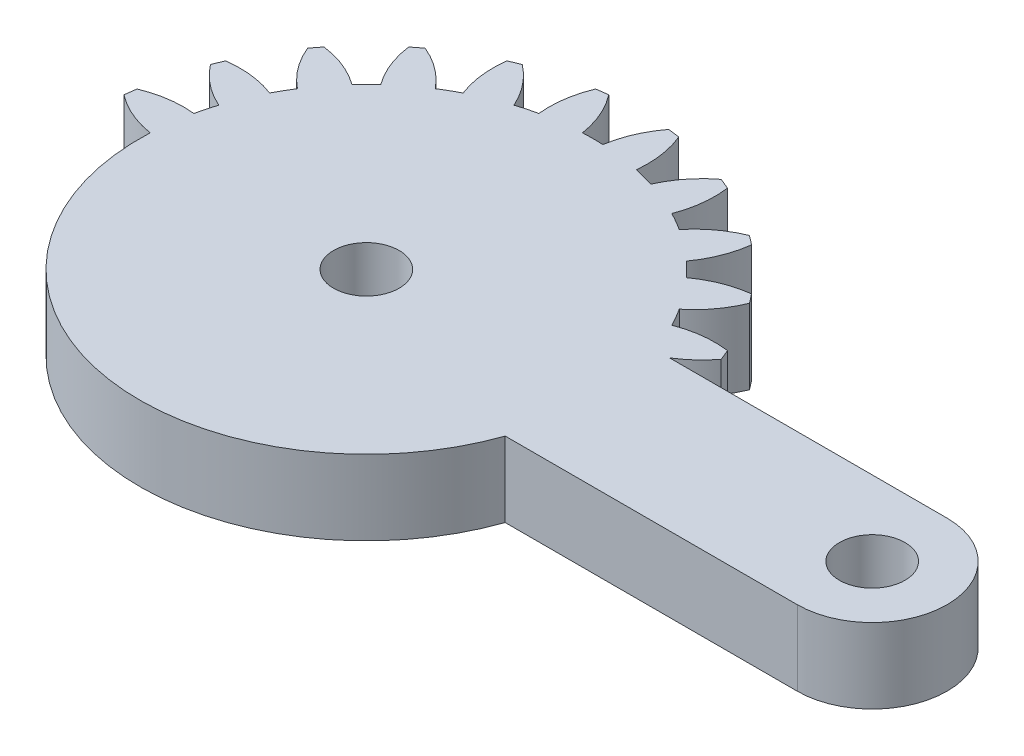
SolidWorks part; units mm, degrees
ref_plane "Front Plane" through (0, 0, 0) normal (0, 0, 1) x (1, 0, 0)
ref_plane "Top Plane" through (0, 0, 0) normal (0, 1, 0) x (1, 0, 0)
ref_plane "Right Plane" through (0, 0, 0) normal (1, 0, 0) x (0, 0, -1)
sketch "Sketch1" plane through (0, 0, 0) normal (0, 1, 0) x (1, 0, 0)
  line L0 (16.8937, 4) -> (2.0816, 4)
  line L1 (2.0816, -4) -> (16.8937, -4)
  line L2 (-10.1063, 0) -> (47.0285, 0) construction
  arc A0 (2.0816, 4) -> (3.5217, 5.3071) centre (-0.7683, 8.5867) ccw
  arc A1 (3.5217, 5.3071) -> (3.2829, 5.8838) centre (-10.1063, 0) ccw
  arc A2 (3.2829, 5.8838) -> (0.6271, 5.5703) centre (2.5684, 0.5313) ccw
  arc A3 (0.6271, 5.5703) -> (0.0844, 6.5103) centre (-10.1063, 0) ccw
  arc A4 (0.0844, 6.5103) -> (1.6838, 8.6535) centre (-3.3089, 10.711) ccw
  arc A5 (1.6838, 8.6535) -> (1.3038, 9.1487) centre (-10.1063, 0) ccw
  arc A6 (1.3038, 9.1487) -> (-1.1803, 8.1585) centre (1.999, 3.7936) ccw
  arc A7 (-1.1803, 8.1585) -> (-1.9479, 8.926) centre (-10.1063, 0) ccw
  arc A8 (-1.9479, 8.926) -> (-0.9576, 11.4102) centre (-6.3127, 12.1053) ccw
  arc A9 (-0.9576, 11.4102) -> (-1.4528, 11.7901) centre (-10.1063, 0) ccw
  arc A10 (-1.4528, 11.7901) -> (-3.596, 10.1907) centre (0.6046, 6.7975) ccw
  arc A11 (-3.596, 10.1907) -> (-4.5361, 10.7334) centre (-10.1063, 0) ccw
  arc A12 (-4.5361, 10.7334) -> (-4.2225, 13.3892) centre (-9.5751, 12.6747) ccw
  arc A13 (-4.2225, 13.3892) -> (-4.7992, 13.6281) centre (-10.1063, 0) ccw
  arc A14 (-4.7992, 13.6281) -> (-6.4554, 11.5285) centre (-1.5196, 9.3381) ccw
  arc A15 (-6.4554, 11.5285) -> (-7.5039, 11.8094) centre (-10.1063, 0) ccw
  arc A16 (-7.5039, 11.8094) -> (-7.8884, 14.4558) centre (-12.8736, 12.3803) ccw
  arc A17 (-7.8884, 14.4558) -> (-8.5072, 14.5373) centre (-10.1063, 0) ccw
  arc A18 (-8.5072, 14.5373) -> (-9.5636, 12.0806) centre (-4.2291, 11.2423) ccw
  arc A19 (-9.5636, 12.0806) -> (-10.6491, 12.0806) centre (-10.1063, 0) ccw
  arc A20 (-10.6491, 12.0806) -> (-11.7054, 14.5373) centre (-15.9836, 11.2423) ccw
  arc A21 (-11.7054, 14.5373) -> (-12.3243, 14.4558) centre (-10.1063, 0) ccw
  arc A22 (-12.3243, 14.4558) -> (-12.7088, 11.8094) centre (-7.3391, 12.3803) ccw
  arc A23 (-12.7088, 11.8094) -> (-13.7573, 11.5285) centre (-10.1063, 0) ccw
  arc A24 (-13.7573, 11.5285) -> (-15.4135, 13.6281) centre (-18.6931, 9.3381) ccw
  arc A25 (-15.4135, 13.6281) -> (-15.9901, 13.3892) centre (-10.1063, 0) ccw
  arc A26 (-15.9901, 13.3892) -> (-15.6766, 10.7334) centre (-10.6376, 12.6747) ccw
  arc A27 (-15.6766, 10.7334) -> (-16.6166, 10.1907) centre (-10.1063, 0) ccw
  arc A28 (-16.6166, 10.1907) -> (-18.7599, 11.7901) centre (-20.8173, 6.7975) ccw
  arc A29 (-18.7599, 11.7901) -> (-19.255, 11.4102) centre (-10.1063, 0) ccw
  arc A30 (-19.255, 11.4102) -> (-18.2648, 8.926) centre (-13.9, 12.1053) ccw
  arc A31 (-18.2648, 8.926) -> (-19.0324, 8.1585) centre (-10.1063, 0) ccw
  arc A32 (-19.0324, 8.1585) -> (-21.5165, 9.1487) centre (-22.2117, 3.7936) ccw
  arc A33 (-21.5165, 9.1487) -> (-21.8965, 8.6535) centre (-10.1063, 0) ccw
  arc A34 (-21.8965, 8.6535) -> (-20.2971, 6.5103) centre (-16.9038, 10.711) ccw
  arc A35 (-20.2971, 6.5103) -> (-20.8398, 5.5703) centre (-10.1063, 0) ccw
  arc A36 (-20.8398, 5.5703) -> (-23.4956, 5.8838) centre (-22.7811, 0.5313) ccw
  arc A37 (-23.4956, 5.8838) -> (-23.7344, 5.3071) centre (-10.1063, 0) ccw
  arc A38 (-23.7344, 5.3071) -> (-21.6348, 3.6509) centre (-19.4444, 8.5867) ccw
  arc A39 (-21.6348, 3.6509) -> (-21.9157, 2.6025) centre (-10.1063, 0) ccw
  arc A40 (-21.9157, 2.6025) -> (-24.5622, 2.2179) centre (-22.4867, -2.7673) ccw
  arc A41 (-24.5622, 2.2179) -> (-24.6437, 1.5991) centre (-10.1063, 0) ccw
  arc A42 (-24.6437, 1.5991) -> (-22.1869, 0.5427) centre (-21.3486, 5.8773) ccw
  arc A43 (-22.1869, 0.5427) -> (-22.1869, -0.5427) centre (-10.1063, 0) ccw
  arc A44 (-22.1869, -0.5427) -> (-24.6437, -1.5991) centre (-21.3486, -5.8773) ccw
  arc A45 (-24.6437, -1.5991) -> (-24.5622, -2.2179) centre (-10.1063, 0) ccw
  arc A46 (-24.5622, -2.2179) -> (-21.9157, -2.6025) centre (-22.4867, 2.7673) ccw
  arc A47 (-21.9157, -2.6025) -> (-21.6348, -3.6509) centre (-10.1063, 0) ccw
  arc A48 (-21.6348, -3.6509) -> (-23.7344, -5.3071) centre (-19.4444, -8.5867) ccw
  arc A49 (-23.7344, -5.3071) -> (-23.4956, -5.8838) centre (-10.1063, 0) ccw
  arc A50 (-23.4956, -5.8838) -> (-20.8398, -5.5703) centre (-22.7811, -0.5313) ccw
  arc A51 (-20.8398, -5.5703) -> (-20.2971, -6.5103) centre (-10.1063, 0) ccw
  arc A52 (-20.2971, -6.5103) -> (-21.8965, -8.6535) centre (-16.9038, -10.711) ccw
  arc A53 (-21.8965, -8.6535) -> (-21.5165, -9.1487) centre (-10.1063, 0) ccw
  arc A54 (-21.5165, -9.1487) -> (-19.0324, -8.1585) centre (-22.2117, -3.7936) ccw
  arc A55 (-19.0324, -8.1585) -> (-18.2648, -8.926) centre (-10.1063, 0) ccw
  arc A56 (-18.2648, -8.926) -> (-19.255, -11.4102) centre (-13.9, -12.1053) ccw
  arc A57 (-19.255, -11.4102) -> (-18.7599, -11.7901) centre (-10.1063, 0) ccw
  arc A58 (-18.7599, -11.7901) -> (-16.6166, -10.1907) centre (-20.8173, -6.7975) ccw
  arc A59 (-16.6166, -10.1907) -> (-15.6766, -10.7334) centre (-10.1063, 0) ccw
  arc A60 (-15.6766, -10.7334) -> (-15.9901, -13.3892) centre (-10.6376, -12.6747) ccw
  arc A61 (-15.9901, -13.3892) -> (-15.4135, -13.6281) centre (-10.1063, 0) ccw
  arc A62 (-15.4135, -13.6281) -> (-13.7573, -11.5285) centre (-18.6931, -9.3381) ccw
  arc A63 (-13.7573, -11.5285) -> (-12.7088, -11.8094) centre (-10.1063, 0) ccw
  arc A64 (-12.7088, -11.8094) -> (-12.3243, -14.4558) centre (-7.3391, -12.3803) ccw
  arc A65 (-12.3243, -14.4558) -> (-11.7054, -14.5373) centre (-10.1063, 0) ccw
  arc A66 (-11.7054, -14.5373) -> (-10.6491, -12.0806) centre (-15.9836, -11.2423) ccw
  arc A67 (-10.6491, -12.0806) -> (-9.5636, -12.0806) centre (-10.1063, 0) ccw
  arc A68 (-9.5636, -12.0806) -> (-8.5072, -14.5373) centre (-4.2291, -11.2423) ccw
  arc A69 (-8.5072, -14.5373) -> (-7.8884, -14.4558) centre (-10.1063, 0) ccw
  arc A70 (-7.8884, -14.4558) -> (-7.5039, -11.8094) centre (-12.8736, -12.3803) ccw
  arc A71 (-7.5039, -11.8094) -> (-6.4554, -11.5285) centre (-10.1063, 0) ccw
  arc A72 (-6.4554, -11.5285) -> (-4.7992, -13.6281) centre (-1.5196, -9.3381) ccw
  arc A73 (-4.7992, -13.6281) -> (-4.2225, -13.3892) centre (-10.1063, 0) ccw
  arc A74 (-4.2225, -13.3892) -> (-4.5361, -10.7334) centre (-9.5751, -12.6747) ccw
  arc A75 (-4.5361, -10.7334) -> (-3.596, -10.1907) centre (-10.1063, 0) ccw
  arc A76 (-3.596, -10.1907) -> (-1.4528, -11.7901) centre (0.6046, -6.7975) ccw
  arc A77 (-1.4528, -11.7901) -> (-0.9576, -11.4102) centre (-10.1063, 0) ccw
  arc A78 (-0.9576, -11.4102) -> (-1.9479, -8.926) centre (-6.3127, -12.1053) ccw
  arc A79 (-1.9479, -8.926) -> (-1.1803, -8.1585) centre (-10.1063, 0) ccw
  arc A80 (-1.1803, -8.1585) -> (1.3038, -9.1487) centre (1.999, -3.7936) ccw
  arc A81 (1.3038, -9.1487) -> (1.6838, -8.6535) centre (-10.1063, 0) ccw
  arc A82 (1.6838, -8.6535) -> (0.0844, -6.5103) centre (-3.3089, -10.711) ccw
  arc A83 (0.0844, -6.5103) -> (0.6271, -5.5703) centre (-10.1063, 0) ccw
  arc A84 (0.6271, -5.5703) -> (3.2829, -5.8838) centre (2.5684, -0.5313) ccw
  arc A85 (3.2829, -5.8838) -> (3.5217, -5.3071) centre (-10.1063, 0) ccw
  arc A86 (3.5217, -5.3071) -> (2.0816, -4) centre (-0.7683, -8.5867) ccw
  circle A88 centre (-10.1063, 0) radius 1.75
  circle A90 centre (16.8937, 0) radius 1.75
  arc A91 (16.8937, -4) -> (16.8937, 4) centre (16.8937, 0) ccw
  dimension "D1" = 3.5
  dimension "D3" = 3.5
  dimension "D4" = 27
extrude "Boss-Extrude1" add sketch "Sketch1" along normal blind 4
sketch "Sketch2" plane through (0, 4, 0) normal (0, 1, 0) x (1, 0, 0)
  line L0 (2.0816, -4) -> (1.3057, -4)
  line L2 (16.8937, 4) -> (2.0816, 4)
  line L3 (2.0816, -4) -> (16.8937, -4)
  line L4 (16.8937, 4) -> (2.0816, 4)
  line L5 (2.0816, -4) -> (16.8937, -4)
  circle A0 centre (-10.1063, 0) radius 12.0927
  arc A88 (16.8937, -4) -> (16.8937, 4) centre (16.8937, 0) ccw
  arc A89 (2.0816, 4) -> (3.5217, 5.3071) centre (-0.7683, 8.5867) ccw
  arc A90 (3.5217, 5.3071) -> (3.2829, 5.8838) centre (-10.1063, 0) ccw
  arc A91 (3.2829, 5.8838) -> (0.6271, 5.5703) centre (2.5684, 0.5313) ccw
  arc A92 (0.6271, 5.5703) -> (0.0844, 6.5103) centre (-10.1063, 0) ccw
  arc A93 (0.0844, 6.5103) -> (1.6838, 8.6535) centre (-3.3089, 10.711) ccw
  arc A94 (1.6838, 8.6535) -> (1.3038, 9.1487) centre (-10.1063, 0) ccw
  arc A95 (1.3038, 9.1487) -> (-1.1803, 8.1585) centre (1.999, 3.7936) ccw
  arc A96 (-1.1803, 8.1585) -> (-1.9479, 8.926) centre (-10.1063, 0) ccw
  arc A97 (-1.9479, 8.926) -> (-0.9576, 11.4102) centre (-6.3127, 12.1053) ccw
  arc A98 (-0.9576, 11.4102) -> (-1.4528, 11.7901) centre (-10.1063, 0) ccw
  arc A99 (-1.4528, 11.7901) -> (-3.596, 10.1907) centre (0.6046, 6.7975) ccw
  arc A100 (-3.596, 10.1907) -> (-4.5361, 10.7334) centre (-10.1063, 0) ccw
  arc A101 (-4.5361, 10.7334) -> (-4.2225, 13.3892) centre (-9.5751, 12.6747) ccw
  arc A102 (-4.2225, 13.3892) -> (-4.7992, 13.6281) centre (-10.1063, 0) ccw
  arc A103 (-4.7992, 13.6281) -> (-6.4554, 11.5285) centre (-1.5196, 9.3381) ccw
  arc A104 (-6.4554, 11.5285) -> (-7.5039, 11.8094) centre (-10.1063, 0) ccw
  arc A105 (-7.5039, 11.8094) -> (-7.8884, 14.4558) centre (-12.8736, 12.3803) ccw
  arc A106 (-7.8884, 14.4558) -> (-8.5072, 14.5373) centre (-10.1063, 0) ccw
  arc A107 (-8.5072, 14.5373) -> (-9.5636, 12.0806) centre (-4.2291, 11.2423) ccw
  arc A108 (-9.5636, 12.0806) -> (-10.6491, 12.0806) centre (-10.1063, 0) ccw
  arc A109 (-10.6491, 12.0806) -> (-11.7054, 14.5373) centre (-15.9836, 11.2423) ccw
  arc A110 (-11.7054, 14.5373) -> (-12.3243, 14.4558) centre (-10.1063, 0) ccw
  arc A111 (-12.3243, 14.4558) -> (-12.7088, 11.8094) centre (-7.3391, 12.3803) ccw
  arc A112 (-12.7088, 11.8094) -> (-13.7573, 11.5285) centre (-10.1063, 0) ccw
  arc A113 (-13.7573, 11.5285) -> (-15.4135, 13.6281) centre (-18.6931, 9.3381) ccw
  arc A114 (-15.4135, 13.6281) -> (-15.9901, 13.3892) centre (-10.1063, 0) ccw
  arc A115 (-15.9901, 13.3892) -> (-15.6766, 10.7334) centre (-10.6376, 12.6747) ccw
  arc A116 (-15.6766, 10.7334) -> (-16.6166, 10.1907) centre (-10.1063, 0) ccw
  arc A117 (-16.6166, 10.1907) -> (-18.7599, 11.7901) centre (-20.8173, 6.7975) ccw
  arc A118 (-18.7599, 11.7901) -> (-19.255, 11.4102) centre (-10.1063, 0) ccw
  arc A119 (-19.255, 11.4102) -> (-18.2648, 8.926) centre (-13.9, 12.1053) ccw
  arc A120 (-18.2648, 8.926) -> (-19.0324, 8.1585) centre (-10.1063, 0) ccw
  arc A121 (-19.0324, 8.1585) -> (-21.5165, 9.1487) centre (-22.2117, 3.7936) ccw
  arc A122 (-21.5165, 9.1487) -> (-21.8965, 8.6535) centre (-10.1063, 0) ccw
  arc A123 (-21.8965, 8.6535) -> (-20.2971, 6.5103) centre (-16.9038, 10.711) ccw
  arc A124 (-20.2971, 6.5103) -> (-20.8398, 5.5703) centre (-10.1063, 0) ccw
  arc A125 (-20.8398, 5.5703) -> (-23.4956, 5.8838) centre (-22.7811, 0.5313) ccw
  arc A126 (-23.4956, 5.8838) -> (-23.7344, 5.3071) centre (-10.1063, 0) ccw
  arc A127 (-23.7344, 5.3071) -> (-21.6348, 3.6509) centre (-19.4444, 8.5867) ccw
  arc A128 (-21.6348, 3.6509) -> (-21.9157, 2.6025) centre (-10.1063, 0) ccw
  arc A129 (-21.9157, 2.6025) -> (-24.5622, 2.2179) centre (-22.4867, -2.7673) ccw
  arc A130 (-24.5622, 2.2179) -> (-24.6437, 1.5991) centre (-10.1063, 0) ccw
  arc A131 (-24.6437, 1.5991) -> (-22.1869, 0.5427) centre (-21.3486, 5.8773) ccw
  arc A132 (-22.1869, 0.5427) -> (-22.1869, -0.5427) centre (-10.1063, 0) ccw
  arc A133 (-22.1869, -0.5427) -> (-24.6437, -1.5991) centre (-21.3486, -5.8773) ccw
  arc A134 (-24.6437, -1.5991) -> (-24.5622, -2.2179) centre (-10.1063, 0) ccw
  arc A135 (-24.5622, -2.2179) -> (-21.9157, -2.6025) centre (-22.4867, 2.7673) ccw
  arc A136 (-21.9157, -2.6025) -> (-21.6348, -3.6509) centre (-10.1063, 0) ccw
  arc A137 (-21.6348, -3.6509) -> (-23.7344, -5.3071) centre (-19.4444, -8.5867) ccw
  arc A138 (-23.7344, -5.3071) -> (-23.4956, -5.8838) centre (-10.1063, 0) ccw
  arc A139 (-23.4956, -5.8838) -> (-20.8398, -5.5703) centre (-22.7811, -0.5313) ccw
  arc A140 (-20.8398, -5.5703) -> (-20.2971, -6.5103) centre (-10.1063, 0) ccw
  arc A141 (-20.2971, -6.5103) -> (-21.8965, -8.6535) centre (-16.9038, -10.711) ccw
  arc A142 (-21.8965, -8.6535) -> (-21.5165, -9.1487) centre (-10.1063, 0) ccw
  arc A143 (-21.5165, -9.1487) -> (-19.0324, -8.1585) centre (-22.2117, -3.7936) ccw
  arc A144 (-19.0324, -8.1585) -> (-18.2648, -8.926) centre (-10.1063, 0) ccw
  arc A145 (-18.2648, -8.926) -> (-19.255, -11.4102) centre (-13.9, -12.1053) ccw
  arc A146 (-19.255, -11.4102) -> (-18.7599, -11.7901) centre (-10.1063, 0) ccw
  arc A147 (-18.7599, -11.7901) -> (-16.6166, -10.1907) centre (-20.8173, -6.7975) ccw
  arc A148 (-16.6166, -10.1907) -> (-15.6766, -10.7334) centre (-10.1063, 0) ccw
  arc A149 (-15.6766, -10.7334) -> (-15.9901, -13.3892) centre (-10.6376, -12.6747) ccw
  arc A150 (-15.9901, -13.3892) -> (-15.4135, -13.6281) centre (-10.1063, 0) ccw
  arc A151 (-15.4135, -13.6281) -> (-13.7573, -11.5285) centre (-18.6931, -9.3381) ccw
  arc A152 (-13.7573, -11.5285) -> (-12.7088, -11.8094) centre (-10.1063, 0) ccw
  arc A153 (-12.7088, -11.8094) -> (-12.3243, -14.4558) centre (-7.3391, -12.3803) ccw
  arc A154 (-12.3243, -14.4558) -> (-11.7054, -14.5373) centre (-10.1063, 0) ccw
  arc A155 (-11.7054, -14.5373) -> (-10.6491, -12.0806) centre (-15.9836, -11.2423) ccw
  arc A156 (-10.6491, -12.0806) -> (-9.5636, -12.0806) centre (-10.1063, 0) ccw
  arc A157 (-9.5636, -12.0806) -> (-8.5072, -14.5373) centre (-4.2291, -11.2423) ccw
  arc A158 (-8.5072, -14.5373) -> (-7.8884, -14.4558) centre (-10.1063, 0) ccw
  arc A159 (-7.8884, -14.4558) -> (-7.5039, -11.8094) centre (-12.8736, -12.3803) ccw
  arc A160 (-7.5039, -11.8094) -> (-6.4554, -11.5285) centre (-10.1063, 0) ccw
  arc A161 (-6.4554, -11.5285) -> (-4.7992, -13.6281) centre (-1.5196, -9.3381) ccw
  arc A162 (-4.7992, -13.6281) -> (-4.2225, -13.3892) centre (-10.1063, 0) ccw
  arc A163 (-4.2225, -13.3892) -> (-4.5361, -10.7334) centre (-9.5751, -12.6747) ccw
  arc A164 (-4.5361, -10.7334) -> (-3.596, -10.1907) centre (-10.1063, 0) ccw
  arc A165 (-3.596, -10.1907) -> (-1.4528, -11.7901) centre (0.6046, -6.7975) ccw
  arc A166 (-1.4528, -11.7901) -> (-0.9576, -11.4102) centre (-10.1063, 0) ccw
  arc A167 (-0.9576, -11.4102) -> (-1.9479, -8.926) centre (-6.3127, -12.1053) ccw
  arc A168 (-1.9479, -8.926) -> (-1.1803, -8.1585) centre (-10.1063, 0) ccw
  arc A169 (-1.1803, -8.1585) -> (1.3038, -9.1487) centre (1.999, -3.7936) ccw
  arc A170 (1.3038, -9.1487) -> (1.6838, -8.6535) centre (-10.1063, 0) ccw
  arc A171 (1.6838, -8.6535) -> (0.0844, -6.5103) centre (-3.3089, -10.711) ccw
  arc A172 (0.0844, -6.5103) -> (0.6271, -5.5703) centre (-10.1063, 0) ccw
  arc A173 (0.6271, -5.5703) -> (3.2829, -5.8838) centre (2.5684, -0.5313) ccw
  arc A174 (3.2829, -5.8838) -> (3.5217, -5.3071) centre (-10.1063, 0) ccw
  arc A175 (3.5217, -5.3071) -> (2.0816, -4) centre (-0.7683, -8.5867) ccw
  arc A176 (16.8937, -4) -> (16.8937, 4) centre (16.8937, 0) ccw
  arc A177 (2.0816, 4) -> (3.5217, 5.3071) centre (-0.7683, 8.5867) ccw
  arc A178 (3.5217, 5.3071) -> (3.2829, 5.8838) centre (-10.1063, 0) ccw
  arc A179 (3.2829, 5.8838) -> (0.6271, 5.5703) centre (2.5684, 0.5313) ccw
  arc A180 (0.6271, 5.5703) -> (0.0844, 6.5103) centre (-10.1063, 0) ccw
  arc A181 (0.0844, 6.5103) -> (1.6838, 8.6535) centre (-3.3089, 10.711) ccw
  arc A182 (1.6838, 8.6535) -> (1.3038, 9.1487) centre (-10.1063, 0) ccw
  arc A183 (1.3038, 9.1487) -> (-1.1803, 8.1585) centre (1.999, 3.7936) ccw
  arc A184 (-1.1803, 8.1585) -> (-1.9479, 8.926) centre (-10.1063, 0) ccw
  arc A185 (-1.9479, 8.926) -> (-0.9576, 11.4102) centre (-6.3127, 12.1053) ccw
  arc A186 (-0.9576, 11.4102) -> (-1.4528, 11.7901) centre (-10.1063, 0) ccw
  arc A187 (-1.4528, 11.7901) -> (-3.596, 10.1907) centre (0.6046, 6.7975) ccw
  arc A188 (-3.596, 10.1907) -> (-4.5361, 10.7334) centre (-10.1063, 0) ccw
  arc A189 (-4.5361, 10.7334) -> (-4.2225, 13.3892) centre (-9.5751, 12.6747) ccw
  arc A190 (-4.2225, 13.3892) -> (-4.7992, 13.6281) centre (-10.1063, 0) ccw
  arc A191 (-4.7992, 13.6281) -> (-6.4554, 11.5285) centre (-1.5196, 9.3381) ccw
  arc A192 (-6.4554, 11.5285) -> (-7.5039, 11.8094) centre (-10.1063, 0) ccw
  arc A193 (-7.5039, 11.8094) -> (-7.8884, 14.4558) centre (-12.8736, 12.3803) ccw
  arc A194 (-7.8884, 14.4558) -> (-8.5072, 14.5373) centre (-10.1063, 0) ccw
  arc A195 (-8.5072, 14.5373) -> (-9.5636, 12.0806) centre (-4.2291, 11.2423) ccw
  arc A196 (-9.5636, 12.0806) -> (-10.6491, 12.0806) centre (-10.1063, 0) ccw
  arc A197 (-10.6491, 12.0806) -> (-11.7054, 14.5373) centre (-15.9836, 11.2423) ccw
  arc A198 (-11.7054, 14.5373) -> (-12.3243, 14.4558) centre (-10.1063, 0) ccw
  arc A199 (-12.3243, 14.4558) -> (-12.7088, 11.8094) centre (-7.3391, 12.3803) ccw
  arc A200 (-12.7088, 11.8094) -> (-13.7573, 11.5285) centre (-10.1063, 0) ccw
  arc A201 (-13.7573, 11.5285) -> (-15.4135, 13.6281) centre (-18.6931, 9.3381) ccw
  arc A202 (-15.4135, 13.6281) -> (-15.9901, 13.3892) centre (-10.1063, 0) ccw
  arc A203 (-15.9901, 13.3892) -> (-15.6766, 10.7334) centre (-10.6376, 12.6747) ccw
  arc A204 (-15.6766, 10.7334) -> (-16.6166, 10.1907) centre (-10.1063, 0) ccw
  arc A205 (-16.6166, 10.1907) -> (-18.7599, 11.7901) centre (-20.8173, 6.7975) ccw
  arc A206 (-18.7599, 11.7901) -> (-19.255, 11.4102) centre (-10.1063, 0) ccw
  arc A207 (-19.255, 11.4102) -> (-18.2648, 8.926) centre (-13.9, 12.1053) ccw
  arc A208 (-18.2648, 8.926) -> (-19.0324, 8.1585) centre (-10.1063, 0) ccw
  arc A209 (-19.0324, 8.1585) -> (-21.5165, 9.1487) centre (-22.2117, 3.7936) ccw
  arc A210 (-21.5165, 9.1487) -> (-21.8965, 8.6535) centre (-10.1063, 0) ccw
  arc A211 (-21.8965, 8.6535) -> (-20.2971, 6.5103) centre (-16.9038, 10.711) ccw
  arc A212 (-20.2971, 6.5103) -> (-20.8398, 5.5703) centre (-10.1063, 0) ccw
  arc A213 (-20.8398, 5.5703) -> (-23.4956, 5.8838) centre (-22.7811, 0.5313) ccw
  arc A214 (-23.4956, 5.8838) -> (-23.7344, 5.3071) centre (-10.1063, 0) ccw
  arc A215 (-23.7344, 5.3071) -> (-21.6348, 3.6509) centre (-19.4444, 8.5867) ccw
  arc A216 (-21.6348, 3.6509) -> (-21.9157, 2.6025) centre (-10.1063, 0) ccw
  arc A217 (-21.9157, 2.6025) -> (-24.5622, 2.2179) centre (-22.4867, -2.7673) ccw
  arc A218 (-24.5622, 2.2179) -> (-24.6437, 1.5991) centre (-10.1063, 0) ccw
  arc A219 (-24.6437, 1.5991) -> (-22.1869, 0.5427) centre (-21.3486, 5.8773) ccw
  arc A220 (-22.1869, 0.5427) -> (-22.1869, -0.5427) centre (-10.1063, 0) ccw
  arc A221 (-22.1869, -0.5427) -> (-24.6437, -1.5991) centre (-21.3486, -5.8773) ccw
  arc A222 (-24.6437, -1.5991) -> (-24.5622, -2.2179) centre (-10.1063, 0) ccw
  arc A223 (-24.5622, -2.2179) -> (-21.9157, -2.6025) centre (-22.4867, 2.7673) ccw
  arc A224 (-21.9157, -2.6025) -> (-21.6348, -3.6509) centre (-10.1063, 0) ccw
  arc A225 (-21.6348, -3.6509) -> (-23.7344, -5.3071) centre (-19.4444, -8.5867) ccw
  arc A226 (-23.7344, -5.3071) -> (-23.4956, -5.8838) centre (-10.1063, 0) ccw
  arc A227 (-23.4956, -5.8838) -> (-20.8398, -5.5703) centre (-22.7811, -0.5313) ccw
  arc A228 (-20.8398, -5.5703) -> (-20.2971, -6.5103) centre (-10.1063, 0) ccw
  arc A229 (-20.2971, -6.5103) -> (-21.8965, -8.6535) centre (-16.9038, -10.711) ccw
  arc A230 (-21.8965, -8.6535) -> (-21.5165, -9.1487) centre (-10.1063, 0) ccw
  arc A231 (-21.5165, -9.1487) -> (-19.0324, -8.1585) centre (-22.2117, -3.7936) ccw
  arc A232 (-19.0324, -8.1585) -> (-18.2648, -8.926) centre (-10.1063, 0) ccw
  arc A233 (-18.2648, -8.926) -> (-19.255, -11.4102) centre (-13.9, -12.1053) ccw
  arc A234 (-19.255, -11.4102) -> (-18.7599, -11.7901) centre (-10.1063, 0) ccw
  arc A235 (-18.7599, -11.7901) -> (-16.6166, -10.1907) centre (-20.8173, -6.7975) ccw
  arc A236 (-16.6166, -10.1907) -> (-15.6766, -10.7334) centre (-10.1063, 0) ccw
  arc A237 (-15.6766, -10.7334) -> (-15.9901, -13.3892) centre (-10.6376, -12.6747) ccw
  arc A238 (-15.9901, -13.3892) -> (-15.4135, -13.6281) centre (-10.1063, 0) ccw
  arc A239 (-15.4135, -13.6281) -> (-13.7573, -11.5285) centre (-18.6931, -9.3381) ccw
  arc A240 (-13.7573, -11.5285) -> (-12.7088, -11.8094) centre (-10.1063, 0) ccw
  arc A241 (-12.7088, -11.8094) -> (-12.3243, -14.4558) centre (-7.3391, -12.3803) ccw
  arc A242 (-12.3243, -14.4558) -> (-11.7054, -14.5373) centre (-10.1063, 0) ccw
  arc A243 (-11.7054, -14.5373) -> (-10.6491, -12.0806) centre (-15.9836, -11.2423) ccw
  arc A244 (-10.6491, -12.0806) -> (-9.5636, -12.0806) centre (-10.1063, 0) ccw
  arc A245 (-9.5636, -12.0806) -> (-8.5072, -14.5373) centre (-4.2291, -11.2423) ccw
  arc A246 (-8.5072, -14.5373) -> (-7.8884, -14.4558) centre (-10.1063, 0) ccw
  arc A247 (-7.8884, -14.4558) -> (-7.5039, -11.8094) centre (-12.8736, -12.3803) ccw
  arc A248 (-7.5039, -11.8094) -> (-6.4554, -11.5285) centre (-10.1063, 0) ccw
  arc A249 (-6.4554, -11.5285) -> (-4.7992, -13.6281) centre (-1.5196, -9.3381) ccw
  arc A250 (-4.7992, -13.6281) -> (-4.2225, -13.3892) centre (-10.1063, 0) ccw
  arc A251 (-4.2225, -13.3892) -> (-4.5361, -10.7334) centre (-9.5751, -12.6747) ccw
  arc A252 (-4.5361, -10.7334) -> (-3.596, -10.1907) centre (-10.1063, 0) ccw
  arc A253 (-3.596, -10.1907) -> (-1.4528, -11.7901) centre (0.6046, -6.7975) ccw
  arc A254 (-1.4528, -11.7901) -> (-0.9576, -11.4102) centre (-10.1063, 0) ccw
  arc A255 (-0.9576, -11.4102) -> (-1.9479, -8.926) centre (-6.3127, -12.1053) ccw
  arc A256 (-1.9479, -8.926) -> (-1.1803, -8.1585) centre (-10.1063, 0) ccw
  arc A257 (-1.1803, -8.1585) -> (1.3038, -9.1487) centre (1.999, -3.7936) ccw
  arc A258 (1.3038, -9.1487) -> (1.6838, -8.6535) centre (-10.1063, 0) ccw
  arc A259 (1.6838, -8.6535) -> (0.0844, -6.5103) centre (-3.3089, -10.711) ccw
  arc A260 (0.0844, -6.5103) -> (0.6271, -5.5703) centre (-10.1063, 0) ccw
  arc A261 (0.6271, -5.5703) -> (3.2829, -5.8838) centre (2.5684, -0.5313) ccw
  arc A262 (3.2829, -5.8838) -> (3.5217, -5.3071) centre (-10.1063, 0) ccw
  arc A263 (3.5217, -5.3071) -> (2.0816, -4) centre (-0.7683, -8.5867) ccw
  dimension "D1" = 0
extrude "Cut-Extrude1" cut sketch "Sketch2" against normal blind 10 contours A222 A223 A0 A221 | A226 A227 A0 A225 | A230 A231 A0 A229 | A234 A235 A0 A233 | A238 A239 A0 A237 | A242 A243 A0 A241 | A246 A247 A0 A245 | A250 A251 A0 A249 | A254 A255 A0 A253 | A258 A259 A0 A257 | A262 A263 L0 A0 A261
